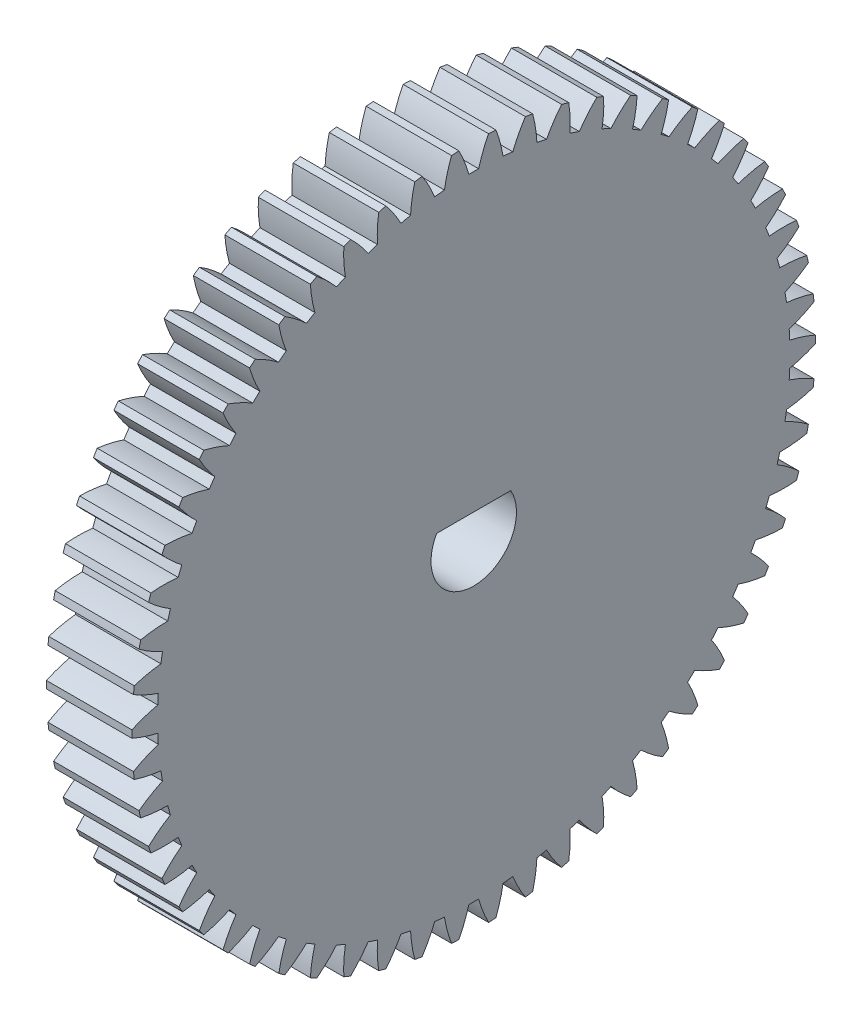
SolidWorks part; units mm, degrees
ref_plane "Front Plane" through (0, 0, 0) normal (0, 0, 1) x (1, 0, 0)
ref_plane "Top Plane" through (0, 0, 0) normal (0, 1, 0) x (1, 0, 0)
ref_plane "Right Plane" through (0, 0, 0) normal (1, 0, 0) x (0, 0, -1)
ref_plane "Plane4" through (6, 0, 0) normal (1, 0, 0) x (0, 0, -1)
sketch "Sketch1" plane through (6, 0, 0) normal (1, 0, 0) x (0, 0, -1)
  arc A0 (2.7423, 22.029) -> (2.0574, 22.1035) centre (0, 0) ccw
  arc A1 (2.0574, 22.1035) -> (1.5571, 23.9494) centre (-7.1019, 20.6117) ccw
  arc A2 (1.5571, 23.9494) -> (1.0414, 23.9774) centre (0, 0) ccw
  arc A3 (1.0414, 23.9774) -> (0.3444, 22.1963) centre (9.2888, 19.723) ccw
  arc A4 (0.3444, 22.1963) -> (-0.3444, 22.1963) centre (0, 0) ccw
  arc A5 (-0.3444, 22.1963) -> (-1.0414, 23.9774) centre (-9.2888, 19.723) ccw
  arc A6 (-1.0414, 23.9774) -> (-1.5571, 23.9494) centre (0, 0) ccw
  arc A7 (-1.5571, 23.9494) -> (-2.0574, 22.1035) centre (7.1019, 20.6117) ccw
  arc A8 (-2.0574, 22.1035) -> (-2.7423, 22.029) centre (0, 0) ccw
  arc A9 (-2.7423, 22.029) -> (-3.6277, 23.7242) centre (-11.3668, 18.6031) ccw
  arc A10 (-3.6277, 23.7242) -> (-4.1373, 23.6407) centre (0, 0) ccw
  arc A11 (-4.1373, 23.6407) -> (-4.4352, 21.7514) centre (4.8317, 21.2587) ccw
  arc A12 (-4.4352, 21.7514) -> (-5.1079, 21.6033) centre (0, 0) ccw
  arc A13 (-5.1079, 21.6033) -> (-6.1715, 23.1929) centre (-13.3115, 17.2651) ccw
  arc A14 (-6.1715, 23.1929) -> (-6.6691, 23.0548) centre (0, 0) ccw
  arc A15 (-6.6691, 23.0548) -> (-6.7609, 21.1444) centre (2.5049, 21.6565) ccw
  arc A16 (-6.7609, 21.1444) -> (-7.4137, 20.9244) centre (0, 0) ccw
  arc A17 (-7.4137, 20.9244) -> (-8.6429, 22.3897) centre (-15.1001, 15.7246) ccw
  arc A18 (-8.6429, 22.3897) -> (-9.1227, 22.1986) centre (0, 0) ccw
  arc A19 (-9.1227, 22.1986) -> (-9.0074, 20.2895) centre (0.1488, 21.8004) ccw
  arc A20 (-9.0074, 20.2895) -> (-9.6326, 20.0002) centre (0, 0) ccw
  arc A21 (-9.6326, 20.0002) -> (-11.013, 21.324) centre (-16.7117, 13.9999) ccw
  arc A22 (-11.013, 21.324) -> (-11.4693, 21.0821) centre (0, 0) ccw
  arc A23 (-11.4693, 21.0821) -> (-11.1483, 19.1967) centre (-2.2091, 21.6887) ccw
  arc A24 (-11.1483, 19.1967) -> (-11.7385, 18.8415) centre (0, 0) ccw
  arc A25 (-11.7385, 18.8415) -> (-13.254, 20.0083) centre (-18.1274, 12.1109) ccw
  arc A26 (-13.254, 20.0083) -> (-13.6814, 19.7185) centre (0, 0) ccw
  arc A27 (-13.6814, 19.7185) -> (-13.1584, 17.8788) centre (-4.5411, 21.3227) ccw
  arc A28 (-13.1584, 17.8788) -> (-13.7069, 17.4619) centre (0, 0) ccw
  arc A29 (-13.7069, 17.4619) -> (-15.3396, 18.458) centre (-19.3306, 10.08) ccw
  arc A30 (-15.3396, 18.458) -> (-15.7332, 18.1237) centre (0, 0) ccw
  arc A31 (-15.7332, 18.1237) -> (-15.0143, 16.3513) centre (-6.8199, 20.7067) ccw
  arc A32 (-15.0143, 16.3513) -> (-15.5145, 15.8776) centre (0, 0) ccw
  arc A33 (-15.5145, 15.8776) -> (-17.2453, 16.6913) centre (-20.3071, 7.9309) ccw
  arc A34 (-17.2453, 16.6913) -> (-17.6004, 16.3164) centre (0, 0) ccw
  arc A35 (-17.6004, 16.3164) -> (-16.6942, 14.6321) centre (-9.0187, 19.8479) ccw
  arc A36 (-16.6942, 14.6321) -> (-17.1402, 14.1071) centre (0, 0) ccw
  arc A37 (-17.1402, 14.1071) -> (-18.9489, 14.7289) centre (-21.0455, 5.6888) ccw
  arc A38 (-18.9489, 14.7289) -> (-19.2614, 14.3178) centre (0, 0) ccw
  arc A39 (-19.2614, 14.3178) -> (-18.1784, 12.7414) centre (-11.1118, 18.7565) ccw
  arc A40 (-18.1784, 12.7414) -> (-18.565, 12.1712) centre (0, 0) ccw
  arc A41 (-18.565, 12.1712) -> (-20.4303, 12.5938) centre (-21.5372, 3.3801) ccw
  arc A42 (-20.4303, 12.5938) -> (-20.6965, 12.1513) centre (0, 0) ccw
  arc A43 (-20.6965, 12.1513) -> (-19.4494, 10.7013) centre (-13.0746, 17.4452) ccw
  arc A44 (-19.4494, 10.7013) -> (-19.7721, 10.0926) centre (0, 0) ccw
  arc A45 (-19.7721, 10.0926) -> (-21.6721, 10.3111) centre (-21.7764, 1.0317) ccw
  arc A46 (-21.6721, 10.3111) -> (-21.889, 9.8424) centre (0, 0) ccw
  arc A47 (-21.889, 9.8424) -> (-20.4924, 8.5357) centre (-14.8841, 15.9293) ccw
  arc A48 (-20.4924, 8.5357) -> (-20.7474, 7.8957) centre (0, 0) ccw
  arc A49 (-20.7474, 7.8957) -> (-22.6599, 7.9075) centre (-21.7603, -1.3288) ccw
  arc A50 (-22.6599, 7.9075) -> (-22.8248, 7.4181) centre (0, 0) ccw
  arc A51 (-22.8248, 7.4181) -> (-21.2951, 6.27) centre (-16.5191, 14.2267) ccw
  arc A52 (-21.2951, 6.27) -> (-21.4794, 5.6063) centre (0, 0) ccw
  arc A53 (-21.4794, 5.6063) -> (-23.382, 5.4112) centre (-21.4891, -3.6737) ccw
  arc A54 (-23.382, 5.4112) -> (-23.493, 4.9068) centre (0, 0) ccw
  arc A55 (-23.493, 4.9068) -> (-21.8482, 3.9309) centre (-17.9604, 12.3572) ccw
  arc A56 (-21.8482, 3.9309) -> (-21.9596, 3.2511) centre (0, 0) ccw
  arc A57 (-21.9596, 3.2511) -> (-23.83, 2.8514) centre (-20.9659, -5.9756) ccw
  arc A58 (-23.83, 2.8514) -> (-23.8858, 2.338) centre (0, 0) ccw
  arc A59 (-23.8858, 2.338) -> (-22.1451, 1.5456) centre (-19.1912, 10.3429) ccw
  arc A60 (-22.1451, 1.5456) -> (-22.1824, 0.8577) centre (0, 0) ccw
  arc A61 (-22.1824, 0.8577) -> (-23.9986, 0.2582) centre (-20.197, -8.2074) ccw
  arc A62 (-23.9986, 0.2582) -> (-23.9986, -0.2582) centre (0, 0) ccw
  arc A63 (-23.9986, -0.2582) -> (-22.1824, -0.8577) centre (-20.197, 8.2074) ccw
  arc A64 (-22.1824, -0.8577) -> (-22.1451, -1.5456) centre (0, 0) ccw
  arc A65 (-22.1451, -1.5456) -> (-23.8858, -2.338) centre (-19.1912, -10.3429) ccw
  arc A66 (-23.8858, -2.338) -> (-23.83, -2.8514) centre (0, 0) ccw
  arc A67 (-23.83, -2.8514) -> (-21.9596, -3.2511) centre (-20.9659, 5.9756) ccw
  arc A68 (-21.9596, -3.2511) -> (-21.8482, -3.9309) centre (0, 0) ccw
  arc A69 (-21.8482, -3.9309) -> (-23.493, -4.9068) centre (-17.9604, -12.3572) ccw
  arc A70 (-23.493, -4.9068) -> (-23.382, -5.4112) centre (0, 0) ccw
  arc A71 (-23.382, -5.4112) -> (-21.4794, -5.6063) centre (-21.4891, 3.6737) ccw
  arc A72 (-21.4794, -5.6063) -> (-21.2951, -6.27) centre (0, 0) ccw
  arc A73 (-21.2951, -6.27) -> (-22.8248, -7.4181) centre (-16.5191, -14.2267) ccw
  arc A74 (-22.8248, -7.4181) -> (-22.6599, -7.9075) centre (0, 0) ccw
  arc A75 (-22.6599, -7.9075) -> (-20.7474, -7.8957) centre (-21.7603, 1.3288) ccw
  arc A76 (-20.7474, -7.8957) -> (-20.4924, -8.5357) centre (0, 0) ccw
  arc A77 (-20.4924, -8.5357) -> (-21.889, -9.8424) centre (-14.8841, -15.9293) ccw
  arc A78 (-21.889, -9.8424) -> (-21.6721, -10.3111) centre (0, 0) ccw
  arc A79 (-21.6721, -10.3111) -> (-19.7721, -10.0926) centre (-21.7764, -1.0317) ccw
  arc A80 (-19.7721, -10.0926) -> (-19.4494, -10.7013) centre (0, 0) ccw
  arc A81 (-19.4494, -10.7013) -> (-20.6965, -12.1513) centre (-13.0746, -17.4452) ccw
  arc A82 (-20.6965, -12.1513) -> (-20.4303, -12.5938) centre (0, 0) ccw
  arc A83 (-20.4303, -12.5938) -> (-18.565, -12.1712) centre (-21.5372, -3.3801) ccw
  arc A84 (-18.565, -12.1712) -> (-18.1784, -12.7414) centre (0, 0) ccw
  arc A85 (-18.1784, -12.7414) -> (-19.2614, -14.3178) centre (-11.1118, -18.7565) ccw
  arc A86 (-19.2614, -14.3178) -> (-18.9489, -14.7289) centre (0, 0) ccw
  arc A87 (-18.9489, -14.7289) -> (-17.1402, -14.1071) centre (-21.0455, -5.6888) ccw
  arc A88 (-17.1402, -14.1071) -> (-16.6942, -14.6321) centre (0, 0) ccw
  arc A89 (-16.6942, -14.6321) -> (-17.6004, -16.3164) centre (-9.0187, -19.8479) ccw
  arc A90 (-17.6004, -16.3164) -> (-17.2453, -16.6913) centre (0, 0) ccw
  arc A91 (-17.2453, -16.6913) -> (-15.5145, -15.8776) centre (-20.3071, -7.9309) ccw
  arc A92 (-15.5145, -15.8776) -> (-15.0143, -16.3513) centre (0, 0) ccw
  arc A93 (-15.0143, -16.3513) -> (-15.7332, -18.1237) centre (-6.8199, -20.7067) ccw
  arc A94 (-15.7332, -18.1237) -> (-15.3396, -18.458) centre (0, 0) ccw
  arc A95 (-15.3396, -18.458) -> (-13.7069, -17.4619) centre (-19.3306, -10.08) ccw
  arc A96 (-13.7069, -17.4619) -> (-13.1584, -17.8788) centre (0, 0) ccw
  arc A97 (-13.1584, -17.8788) -> (-13.6814, -19.7185) centre (-4.5411, -21.3227) ccw
  arc A98 (-13.6814, -19.7185) -> (-13.254, -20.0083) centre (0, 0) ccw
  arc A99 (-13.254, -20.0083) -> (-11.7385, -18.8415) centre (-18.1274, -12.1109) ccw
  arc A100 (-11.7385, -18.8415) -> (-11.1483, -19.1967) centre (0, 0) ccw
  arc A101 (-11.1483, -19.1967) -> (-11.4693, -21.0821) centre (-2.2091, -21.6887) ccw
  arc A102 (-11.4693, -21.0821) -> (-11.013, -21.324) centre (0, 0) ccw
  arc A103 (-11.013, -21.324) -> (-9.6326, -20.0002) centre (-16.7117, -13.9999) ccw
  arc A104 (-9.6326, -20.0002) -> (-9.0074, -20.2895) centre (0, 0) ccw
  arc A105 (-9.0074, -20.2895) -> (-9.1227, -22.1986) centre (0.1488, -21.8004) ccw
  arc A106 (-9.1227, -22.1986) -> (-8.6429, -22.3897) centre (0, 0) ccw
  arc A107 (-8.6429, -22.3897) -> (-7.4137, -20.9244) centre (-15.1001, -15.7246) ccw
  arc A108 (-7.4137, -20.9244) -> (-6.7609, -21.1444) centre (0, 0) ccw
  arc A109 (-6.7609, -21.1444) -> (-6.6691, -23.0548) centre (2.5049, -21.6565) ccw
  arc A110 (-6.6691, -23.0548) -> (-6.1715, -23.1929) centre (0, 0) ccw
  arc A111 (-6.1715, -23.1929) -> (-5.1079, -21.6033) centre (-13.3115, -17.2651) ccw
  arc A112 (-5.1079, -21.6033) -> (-4.4352, -21.7514) centre (0, 0) ccw
  arc A113 (-4.4352, -21.7514) -> (-4.1373, -23.6407) centre (4.8317, -21.2587) ccw
  arc A114 (-4.1373, -23.6407) -> (-3.6277, -23.7242) centre (0, 0) ccw
  arc A115 (-3.6277, -23.7242) -> (-2.7423, -22.029) centre (-11.3668, -18.6031) ccw
  arc A116 (-2.7423, -22.029) -> (-2.0574, -22.1035) centre (0, 0) ccw
  arc A117 (-2.0574, -22.1035) -> (-1.5571, -23.9494) centre (7.1019, -20.6117) ccw
  arc A118 (-1.5571, -23.9494) -> (-1.0414, -23.9774) centre (0, 0) ccw
  arc A119 (-1.0414, -23.9774) -> (-0.3444, -22.1963) centre (-9.2888, -19.723) ccw
  arc A120 (-0.3444, -22.1963) -> (0.3444, -22.1963) centre (0, 0) ccw
  arc A121 (0.3444, -22.1963) -> (1.0414, -23.9774) centre (9.2888, -19.723) ccw
  arc A122 (1.0414, -23.9774) -> (1.5571, -23.9494) centre (0, 0) ccw
  arc A123 (1.5571, -23.9494) -> (2.0574, -22.1035) centre (-7.1019, -20.6117) ccw
  arc A124 (2.0574, -22.1035) -> (2.7423, -22.029) centre (0, 0) ccw
  arc A125 (2.7423, -22.029) -> (3.6277, -23.7242) centre (11.3668, -18.6031) ccw
  arc A126 (3.6277, -23.7242) -> (4.1373, -23.6407) centre (0, 0) ccw
  arc A127 (4.1373, -23.6407) -> (4.4352, -21.7514) centre (-4.8317, -21.2587) ccw
  arc A128 (4.4352, -21.7514) -> (5.1079, -21.6033) centre (0, 0) ccw
  arc A129 (5.1079, -21.6033) -> (6.1715, -23.1929) centre (13.3115, -17.2651) ccw
  arc A130 (6.1715, -23.1929) -> (6.6691, -23.0548) centre (0, 0) ccw
  arc A131 (6.6691, -23.0548) -> (6.7609, -21.1444) centre (-2.5049, -21.6565) ccw
  arc A132 (6.7609, -21.1444) -> (7.4137, -20.9244) centre (0, 0) ccw
  arc A133 (7.4137, -20.9244) -> (8.6429, -22.3897) centre (15.1001, -15.7246) ccw
  arc A134 (8.6429, -22.3897) -> (9.1227, -22.1986) centre (0, 0) ccw
  arc A135 (9.1227, -22.1986) -> (9.0074, -20.2895) centre (-0.1488, -21.8004) ccw
  arc A136 (9.0074, -20.2895) -> (9.6326, -20.0002) centre (0, 0) ccw
  arc A137 (9.6326, -20.0002) -> (11.013, -21.324) centre (16.7117, -13.9999) ccw
  arc A138 (11.013, -21.324) -> (11.4693, -21.0821) centre (0, 0) ccw
  arc A139 (11.4693, -21.0821) -> (11.1483, -19.1967) centre (2.2091, -21.6887) ccw
  arc A140 (11.1483, -19.1967) -> (11.7385, -18.8415) centre (0, 0) ccw
  arc A141 (11.7385, -18.8415) -> (13.254, -20.0083) centre (18.1274, -12.1109) ccw
  arc A142 (13.254, -20.0083) -> (13.6814, -19.7185) centre (0, 0) ccw
  arc A143 (13.6814, -19.7185) -> (13.1584, -17.8788) centre (4.5411, -21.3227) ccw
  arc A144 (13.1584, -17.8788) -> (13.7069, -17.4619) centre (0, 0) ccw
  arc A145 (13.7069, -17.4619) -> (15.3396, -18.458) centre (19.3306, -10.08) ccw
  arc A146 (15.3396, -18.458) -> (15.7332, -18.1237) centre (0, 0) ccw
  arc A147 (15.7332, -18.1237) -> (15.0143, -16.3513) centre (6.8199, -20.7067) ccw
  arc A148 (15.0143, -16.3513) -> (15.5145, -15.8776) centre (0, 0) ccw
  arc A149 (15.5145, -15.8776) -> (17.2453, -16.6913) centre (20.3071, -7.9309) ccw
  arc A150 (17.2453, -16.6913) -> (17.6004, -16.3164) centre (0, 0) ccw
  arc A151 (17.6004, -16.3164) -> (16.6942, -14.6321) centre (9.0187, -19.8479) ccw
  arc A152 (16.6942, -14.6321) -> (17.1402, -14.1071) centre (0, 0) ccw
  arc A153 (17.1402, -14.1071) -> (18.9489, -14.7289) centre (21.0455, -5.6888) ccw
  arc A154 (18.9489, -14.7289) -> (19.2614, -14.3178) centre (0, 0) ccw
  arc A155 (19.2614, -14.3178) -> (18.1784, -12.7414) centre (11.1118, -18.7565) ccw
  arc A156 (18.1784, -12.7414) -> (18.565, -12.1712) centre (0, 0) ccw
  arc A157 (18.565, -12.1712) -> (20.4303, -12.5938) centre (21.5372, -3.3801) ccw
  arc A158 (20.4303, -12.5938) -> (20.6965, -12.1513) centre (0, 0) ccw
  arc A159 (20.6965, -12.1513) -> (19.4494, -10.7013) centre (13.0746, -17.4452) ccw
  arc A160 (19.4494, -10.7013) -> (19.7721, -10.0926) centre (0, 0) ccw
  arc A161 (19.7721, -10.0926) -> (21.6721, -10.3111) centre (21.7764, -1.0317) ccw
  arc A162 (21.6721, -10.3111) -> (21.889, -9.8424) centre (0, 0) ccw
  arc A163 (21.889, -9.8424) -> (20.4924, -8.5357) centre (14.8841, -15.9293) ccw
  arc A164 (20.4924, -8.5357) -> (20.7474, -7.8957) centre (0, 0) ccw
  arc A165 (20.7474, -7.8957) -> (22.6599, -7.9075) centre (21.7603, 1.3288) ccw
  arc A166 (22.6599, -7.9075) -> (22.8248, -7.4181) centre (0, 0) ccw
  arc A167 (22.8248, -7.4181) -> (21.2951, -6.27) centre (16.5191, -14.2267) ccw
  arc A168 (21.2951, -6.27) -> (21.4794, -5.6063) centre (0, 0) ccw
  arc A169 (21.4794, -5.6063) -> (23.382, -5.4112) centre (21.4891, 3.6737) ccw
  arc A170 (23.382, -5.4112) -> (23.493, -4.9068) centre (0, 0) ccw
  arc A171 (23.493, -4.9068) -> (21.8482, -3.9309) centre (17.9604, -12.3572) ccw
  arc A172 (21.8482, -3.9309) -> (21.9596, -3.2511) centre (0, 0) ccw
  arc A173 (21.9596, -3.2511) -> (23.83, -2.8514) centre (20.9659, 5.9756) ccw
  arc A174 (23.83, -2.8514) -> (23.8858, -2.338) centre (0, 0) ccw
  arc A175 (23.8858, -2.338) -> (22.1451, -1.5456) centre (19.1912, -10.3429) ccw
  arc A176 (22.1451, -1.5456) -> (22.1824, -0.8577) centre (0, 0) ccw
  arc A177 (22.1824, -0.8577) -> (23.9986, -0.2582) centre (20.197, 8.2074) ccw
  arc A178 (23.9986, -0.2582) -> (23.9986, 0.2582) centre (0, 0) ccw
  arc A179 (23.9986, 0.2582) -> (22.1824, 0.8577) centre (20.197, -8.2074) ccw
  arc A180 (22.1824, 0.8577) -> (22.1451, 1.5456) centre (0, 0) ccw
  arc A181 (22.1451, 1.5456) -> (23.8858, 2.338) centre (19.1912, 10.3429) ccw
  arc A182 (23.8858, 2.338) -> (23.83, 2.8514) centre (0, 0) ccw
  arc A183 (23.83, 2.8514) -> (21.9596, 3.2511) centre (20.9659, -5.9756) ccw
  arc A184 (21.9596, 3.2511) -> (21.8482, 3.9309) centre (0, 0) ccw
  arc A185 (21.8482, 3.9309) -> (23.493, 4.9068) centre (17.9604, 12.3572) ccw
  arc A186 (23.493, 4.9068) -> (23.382, 5.4112) centre (0, 0) ccw
  arc A187 (23.382, 5.4112) -> (21.4794, 5.6063) centre (21.4891, -3.6737) ccw
  arc A188 (21.4794, 5.6063) -> (21.2951, 6.27) centre (0, 0) ccw
  arc A189 (21.2951, 6.27) -> (22.8248, 7.4181) centre (16.5191, 14.2267) ccw
  arc A190 (22.8248, 7.4181) -> (22.6599, 7.9075) centre (0, 0) ccw
  arc A191 (22.6599, 7.9075) -> (20.7474, 7.8957) centre (21.7603, -1.3288) ccw
  arc A192 (20.7474, 7.8957) -> (20.4924, 8.5357) centre (0, 0) ccw
  arc A193 (20.4924, 8.5357) -> (21.889, 9.8424) centre (14.8841, 15.9293) ccw
  arc A194 (21.889, 9.8424) -> (21.6721, 10.3111) centre (0, 0) ccw
  arc A195 (21.6721, 10.3111) -> (19.7721, 10.0926) centre (21.7764, 1.0317) ccw
  arc A196 (19.7721, 10.0926) -> (19.4494, 10.7013) centre (0, 0) ccw
  arc A197 (19.4494, 10.7013) -> (20.6965, 12.1513) centre (13.0746, 17.4452) ccw
  arc A198 (20.6965, 12.1513) -> (20.4303, 12.5938) centre (0, 0) ccw
  arc A199 (20.4303, 12.5938) -> (18.565, 12.1712) centre (21.5372, 3.3801) ccw
  arc A200 (18.565, 12.1712) -> (18.1784, 12.7414) centre (0, 0) ccw
  arc A201 (18.1784, 12.7414) -> (19.2614, 14.3178) centre (11.1118, 18.7565) ccw
  arc A202 (19.2614, 14.3178) -> (18.9489, 14.7289) centre (0, 0) ccw
  arc A203 (18.9489, 14.7289) -> (17.1402, 14.1071) centre (21.0455, 5.6888) ccw
  arc A204 (17.1402, 14.1071) -> (16.6942, 14.6321) centre (0, 0) ccw
  arc A205 (16.6942, 14.6321) -> (17.6004, 16.3164) centre (9.0187, 19.8479) ccw
  arc A206 (17.6004, 16.3164) -> (17.2453, 16.6913) centre (0, 0) ccw
  arc A207 (17.2453, 16.6913) -> (15.5145, 15.8776) centre (20.3071, 7.9309) ccw
  arc A208 (15.5145, 15.8776) -> (15.0143, 16.3513) centre (0, 0) ccw
  arc A209 (15.0143, 16.3513) -> (15.7332, 18.1237) centre (6.8199, 20.7067) ccw
  arc A210 (15.7332, 18.1237) -> (15.3396, 18.458) centre (0, 0) ccw
  arc A211 (15.3396, 18.458) -> (13.7069, 17.4619) centre (19.3306, 10.08) ccw
  arc A212 (13.7069, 17.4619) -> (13.1584, 17.8788) centre (0, 0) ccw
  arc A213 (13.1584, 17.8788) -> (13.6814, 19.7185) centre (4.5411, 21.3227) ccw
  arc A214 (13.6814, 19.7185) -> (13.254, 20.0083) centre (0, 0) ccw
  arc A215 (13.254, 20.0083) -> (11.7385, 18.8415) centre (18.1274, 12.1109) ccw
  arc A216 (11.7385, 18.8415) -> (11.1483, 19.1967) centre (0, 0) ccw
  arc A217 (11.1483, 19.1967) -> (11.4693, 21.0821) centre (2.2091, 21.6887) ccw
  arc A218 (11.4693, 21.0821) -> (11.013, 21.324) centre (0, 0) ccw
  arc A219 (11.013, 21.324) -> (9.6326, 20.0002) centre (16.7117, 13.9999) ccw
  arc A220 (9.6326, 20.0002) -> (9.0074, 20.2895) centre (0, 0) ccw
  arc A221 (9.0074, 20.2895) -> (9.1227, 22.1986) centre (-0.1488, 21.8004) ccw
  arc A222 (9.1227, 22.1986) -> (8.6429, 22.3897) centre (0, 0) ccw
  arc A223 (8.6429, 22.3897) -> (7.4137, 20.9244) centre (15.1001, 15.7246) ccw
  arc A224 (7.4137, 20.9244) -> (6.7609, 21.1444) centre (0, 0) ccw
  arc A225 (6.7609, 21.1444) -> (6.6691, 23.0548) centre (-2.5049, 21.6565) ccw
  arc A226 (6.6691, 23.0548) -> (6.1715, 23.1929) centre (0, 0) ccw
  arc A227 (6.1715, 23.1929) -> (5.1079, 21.6033) centre (13.3115, 17.2651) ccw
  arc A228 (5.1079, 21.6033) -> (4.4352, 21.7514) centre (0, 0) ccw
  arc A229 (4.4352, 21.7514) -> (4.1373, 23.6407) centre (-4.8317, 21.2587) ccw
  arc A230 (4.1373, 23.6407) -> (3.6277, 23.7242) centre (0, 0) ccw
  arc A231 (3.6277, 23.7242) -> (2.7423, 22.029) centre (11.3668, 18.6031) ccw
  circle A232 centre (0, 0) radius 3
extrude "Boss-Extrude1" add sketch "Sketch1" against normal blind 6
sketch "Sketch2" plane through (6, 0, 0) normal (1, 0, 0) x (0, 0, -1)
  line L0 (-2.5981, 1.5) -> (2.5981, 1.5)
  arc A0 (2.5981, 1.5) -> (-2.5981, 1.5) centre (0, 0) ccw
  dimension "D1" = 6
  dimension "D2" = 1.5
extrude "Boss-Extrude2" add sketch "Sketch2" against normal blind 6 contours L0 A0
